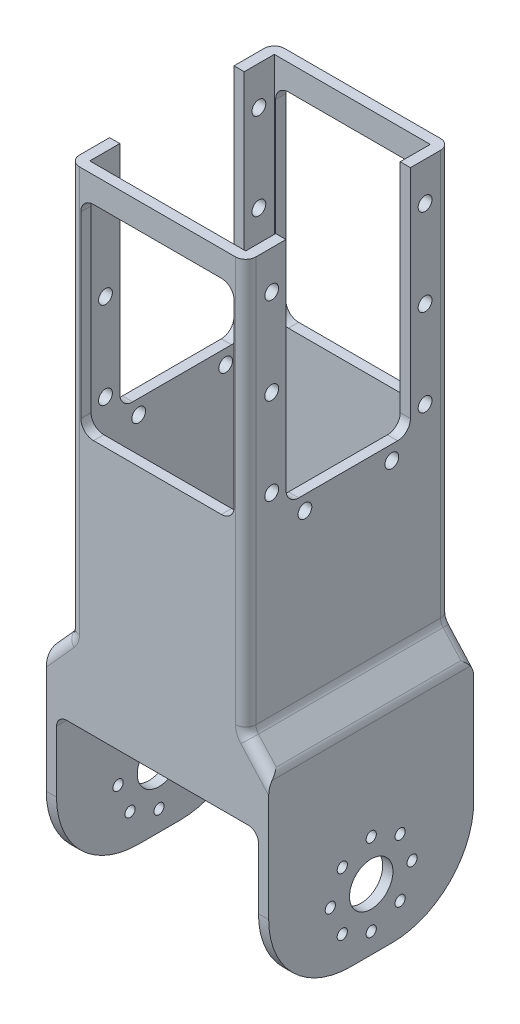
SolidWorks part; units mm, degrees
material "PLA"
ref_plane "Front Plane" through (0, 0, 0) normal (0, 0, 1) x (1, 0, 0)
ref_plane "Top Plane" through (0, 0, 0) normal (0, 1, 0) x (1, 0, 0)
ref_plane "Right Plane" through (0, 0, 0) normal (1, 0, 0) x (0, 0, -1)
sketch "Sketch1" plane through (0, 0, 0) normal (0, 1, 0) x (1, 0, 0)
  line L0 (-19.75, 18.05) -> (19.75, 18.05)
  line L1 (-21.75, -20.05) -> (21.75, -20.05)
  line L2 (-21.75, -20.05) -> (-21.75, 20.05)
  line L3 (-21.75, 20.05) -> (21.75, 20.05)
  line L4 (21.75, -20.05) -> (21.75, 20.05)
  line L5 (-21.75, -20.05) -> (21.75, 20.05) construction
  line L6 (-21.75, 20.05) -> (21.75, -20.05) construction
  line L7 (19.75, -18.05) -> (19.75, 18.05)
  line L8 (-19.75, -18.05) -> (19.75, -18.05)
  line L9 (-19.75, -18.05) -> (-19.75, 18.05)
  point P0 (0, 0)
  dimension "D1" = 43.5
  dimension "D2" = 40.1
  dimension "D3" = 2
extrude "Boss-Extrude1" add sketch "Sketch1" along normal blind 40
sketch "Sketch3" plane through (21.75, 0, 0) normal (1, 0, 0) x (0, 0, -1)
  line L0 (0, 12) -> (0, 0) construction
  line L1 (-20.05, 0) -> (20.05, 0) construction
  circle A0 centre (0, 12) radius 8 construction
  circle A1 centre (0, 20) radius 1
  circle A2 centre (5.6569, 17.6569) radius 1
  circle A3 centre (8, 12) radius 1
  circle A4 centre (5.6569, 6.3431) radius 1
  circle A5 centre (0, 4) radius 1
  circle A6 centre (-5.6569, 6.3431) radius 1
  circle A7 centre (-8, 12) radius 1
  circle A8 centre (-5.6569, 17.6569) radius 1
  circle A9 centre (0, 12) radius 4.25
  point P22 (0, 12)
  dimension "D1" = 16
  dimension "D3" = 2
  dimension "D5" = 8.5
  dimension "D2" = 12
  dimension "D4" = 8
extrude "Cut-Extrude2" cut sketch "Sketch3" against normal through all
sketch "Sketch4" plane through (0, 0, 20.05) normal (0, 0, 1) x (1, 0, 0)
  line L14 (-19.75, 40) -> (-19.75, 0)
  line L15 (-19.75, 30) -> (-19.75, 0)
  line L16 (-19.75, 30) -> (19.75, 30)
  line L17 (19.75, 40) -> (19.75, 0)
  line L18 (19.75, 30) -> (19.75, 0)
  line L19 (-19.75, 0) -> (19.75, 0)
  dimension "D3" = 30
  dimension "D1" = 2
  dimension "D2" = 2
extrude "Cut-Extrude3" cut sketch "Sketch4" against normal through all
fillet "Fillet1" radius 16 4 edges at (-20.75, 0, -20.05) (20.75, 0, -20.05) (20.75, 0, 20.05) (-20.75, 0, 20.05)
ref_plane "Plane1" through (0, 45, 0) normal (0, 1, 0) x (1, 0, 0)
sketch "Sketch7" plane through (0, 45, 0) normal (0, 1, 0) x (1, 0, 0)
  line L0 (-15.25, -18.05) -> (-15.25, 18.05) construction
  line L1 (-17.25, -20.05) -> (17.25, -20.05)
  line L2 (-17.25, -20.05) -> (-17.25, 20.05)
  line L3 (-17.25, 20.05) -> (17.25, 20.05)
  line L4 (17.25, -20.05) -> (17.25, 20.05)
  line L5 (-17.25, -20.05) -> (17.25, 20.05) construction
  line L6 (-17.25, 20.05) -> (17.25, -20.05) construction
  line L7 (-15.25, 18.05) -> (15.25, 18.05) construction
  line L8 (15.25, -18.05) -> (15.25, 18.05) construction
  line L9 (-15.25, -18.05) -> (15.25, -18.05) construction
  point P0 (0, 0)
  dimension "D1" = 34.5
  dimension "D2" = 40.1
  dimension "D3" = 2
sketch "Sketch8" plane through (0, 40, 0) normal (0, 1, 0) x (1, 0, 0)
  line L0 (-21.75, -20.05) -> (21.75, -20.05) construction
  line L1 (-19.75, -18.05) -> (19.75, -18.05) construction
  line L2 (21.75, -20.05) -> (21.75, 20.05) construction
  line L3 (19.75, -18.05) -> (19.75, 18.05) construction
  line L4 (-19.75, 18.05) -> (-19.75, -18.05) construction
  line L5 (19.75, 18.05) -> (-19.75, 18.05) construction
  line L6 (-21.75, 20.05) -> (-21.75, -20.05) construction
  line L7 (21.75, 20.05) -> (-21.75, 20.05) construction
  line L8 (-21.75, -20.05) -> (21.75, -20.05)
  line L9 (-19.75, -18.05) -> (19.75, -18.05) construction
  line L10 (21.75, -20.05) -> (21.75, 20.05)
  line L11 (19.75, -18.05) -> (19.75, 18.05) construction
  line L12 (-19.75, 18.05) -> (-19.75, -18.05) construction
  line L13 (19.75, 18.05) -> (-19.75, 18.05) construction
  line L14 (-21.75, 20.05) -> (-21.75, -20.05)
  line L15 (21.75, 20.05) -> (-21.75, 20.05)
loft "Loft2" add profiles "Sketch8", "Sketch7"
ref_plane "Plane2" through (0, 40, 0) normal (0, 1, 0) x (1, 0, 0)
sketch "Sketch10" plane through (0, 40, 0) normal (0, 1, 0) x (1, 0, 0)
  line L0 (-19.75, -18.05) -> (19.75, -18.05)
  line L1 (19.75, -18.05) -> (19.75, 18.05)
  line L2 (-19.75, 18.05) -> (-19.75, -18.05)
  line L3 (19.75, 18.05) -> (-19.75, 18.05)
  line L4 (-19.75, 18.05) -> (19.75, -18.05) construction
  point P4 (0, 0)
  dimension "D1" = 39.5
  dimension "D2" = 36.1
sketch "Sketch11" plane through (0, 45, 0) normal (0, 1, 0) x (1, 0, 0)
  line L0 (-15.25, -18.05) -> (-15.25, 18.05)
  line L1 (-15.25, 18.05) -> (15.25, 18.05)
  line L2 (15.25, -18.05) -> (15.25, 18.05)
  line L3 (-15.25, -18.05) -> (15.25, -18.05)
  line L4 (-15.25, 18.05) -> (15.25, -18.05) construction
  line L5 (-15.25, -18.05) -> (15.25, 18.05) construction
  point P4 (0, 0)
  dimension "D1" = 36.1
  dimension "D2" = 30.5
loft "Cut-Loft1" cut profiles "Sketch11", "Sketch10"
sketch "Sketch12" plane through (0, 45, 0) normal (0, 1, 0) x (1, 0, 0)
  line L0 (-17.25, 20.05) -> (-17.25, -20.05) construction
  line L1 (-17.25, -20.05) -> (17.25, -20.05) construction
  line L2 (17.25, -20.05) -> (17.25, 20.05) construction
  line L3 (17.25, 20.05) -> (-17.25, 20.05) construction
  line L4 (-17.25, 20.05) -> (-17.25, -20.05)
  line L5 (-17.25, -20.05) -> (17.25, -20.05)
  line L6 (17.25, -20.05) -> (17.25, 20.05)
  line L7 (17.25, 20.05) -> (-17.25, 20.05)
  line L8 (-15.25, -18.05) -> (15.25, -18.05) construction
  line L9 (15.25, -18.05) -> (15.25, 18.05) construction
  line L10 (-15.25, 18.05) -> (-15.25, -18.05) construction
  line L11 (15.25, 18.05) -> (-15.25, 18.05) construction
  line L12 (-15.25, -18.05) -> (15.25, -18.05)
  line L13 (15.25, -18.05) -> (15.25, 18.05)
  line L14 (-15.25, 18.05) -> (-15.25, -18.05)
  line L15 (15.25, 18.05) -> (-15.25, 18.05)
extrude "Boss-Extrude2" add sketch "Sketch12" along normal blind 80
sketch "Sketch5" plane through (-17.25, 0, 0) normal (-1, 0, 0) x (0, 0, 1)
  line L0 (-20.05, 125) -> (20.05, 125) construction
  line L1 (-12.1682, 125) -> (12.1682, 125)
  line L2 (-12.1682, 125) -> (-12.1682, 80)
  line L3 (-12.1682, 80) -> (12.1682, 80)
  line L4 (12.1682, 125) -> (12.1682, 80)
  line L5 (-12.1682, 125) -> (-20.05, 125) construction
  line L6 (-20.05, 40) -> (-20.05, 16) construction
  line L7 (20.05, 125) -> (20.05, 45) construction
  point P6 (0, 0)
  dimension "D1" = 45
  dimension "D2" = 24.3365
  dimension "D3" = 7.8818
extrude "Cut-Extrude4" cut sketch "Sketch5" against normal through all and the other way through all
sketch "Sketch6" plane through (0, 0, 20.05) normal (0, 0, 1) x (1, 0, 0)
  line L0 (-15, 100) -> (-21.75, 100) construction
  line L1 (-15, 80) -> (15, 80)
  line L2 (-15, 80) -> (-15, 120)
  line L3 (-15, 120) -> (15, 120)
  line L4 (15, 80) -> (15, 120)
  line L5 (-15, 80) -> (15, 120) construction
  line L6 (-15, 120) -> (15, 80) construction
  line L7 (-21.75, 40) -> (-21.75, 16) construction
  line L8 (15, 100) -> (21.75, 100) construction
  line L9 (21.75, 40) -> (21.75, 16) construction
  line L10 (0, 100) -> (0, 125) construction
  line L11 (-17.25, 125) -> (17.25, 125) construction
  point P0 (0, 100)
  point P15 (0, 0)
  dimension "D1" = 30
  dimension "D2" = 40
  dimension "D3" = 25
extrude "Cut-Extrude5" cut sketch "Sketch6" against normal through all
fillet "Fillet2" radius 2 16 edges at (-19.75, 30, -19.05) (19.75, 30, -19.05) (19.75, 30, 19.05) (-19.75, 30, 19.05) (21.75, 40, 0) (-21.75, 40, 0)
fillet "Fillet3" radius 2.5 16 edges at (16.25, 80, -12.1682) (16.25, 80, 12.1682) (-15, 120, -19.05) (-15, 80, -19.05) (-16.25, 80, 12.1682) (-16.25, 80, -12.1682) (15, 80, -19.05) (15, 120, -19.05) (15, 120, 19.05) (-15, 120, 19.05) (-15, 80, 19.05) (15, 80, 19.05)
sketch "Sketch16" plane through (-17.25, 0, 0) normal (-1, 0, 0) x (0, 0, 1)
  line L0 (-15.0318, 117.5) -> (-15.0318, 77.2) construction
  line L1 (-15.0318, 77.2) -> (14.9682, 77.2) construction
  line L2 (14.9682, 77.2) -> (14.9682, 117.5) construction
  line L3 (-18.05, 125) -> (-12.1682, 125) construction
  line L4 (12.1682, 125) -> (18.05, 125) construction
  line L5 (-12.1682, 82.5) -> (-12.1682, 125) construction
  circle A1 centre (-15.0318, 117.5) radius 1.35
  circle A3 centre (-15.0318, 100.5) radius 1.35
  circle A5 centre (-15.0318, 83.5) radius 1.35
  circle A7 centre (-8.5318, 77.2) radius 1.35
  circle A9 centre (8.4682, 77.2) radius 1.35
  circle A11 centre (14.9682, 83.5) radius 1.35
  circle A13 centre (14.9682, 100.5) radius 1.35
  circle A15 centre (14.9682, 117.5) radius 1.35
  point P13 (0, 0)
  point P16 (0, 0)
  point P19 (0, 0)
  point P22 (0, 0)
  point P24 (0, 0)
  point P25 (0, 0)
  point P26 (0, 0)
  point P27 (0, 0)
  point P28 (0, 0)
  point P31 (0, 0)
  dimension "D1" = 2.7
  dimension "D2" = 2.7
  dimension "D3" = 2.7
  dimension "D4" = 2.7
  dimension "D5" = 2.7
  dimension "D6" = 2.7
  dimension "D7" = 2.7
  dimension "D8" = 2.7
  dimension "D9" = 7.5
  dimension "D10" = 7.5
  dimension "D11" = 17
  dimension "D12" = 17
  dimension "D13" = 17
  dimension "D14" = 17
  dimension "D15" = 6.5
  dimension "D16" = 17
  dimension "D17" = 6.5
  dimension "D18" = 6.3
  dimension "D19" = 2.8635
extrude "Cut-Extrude6" cut sketch "Sketch16" against normal through all
